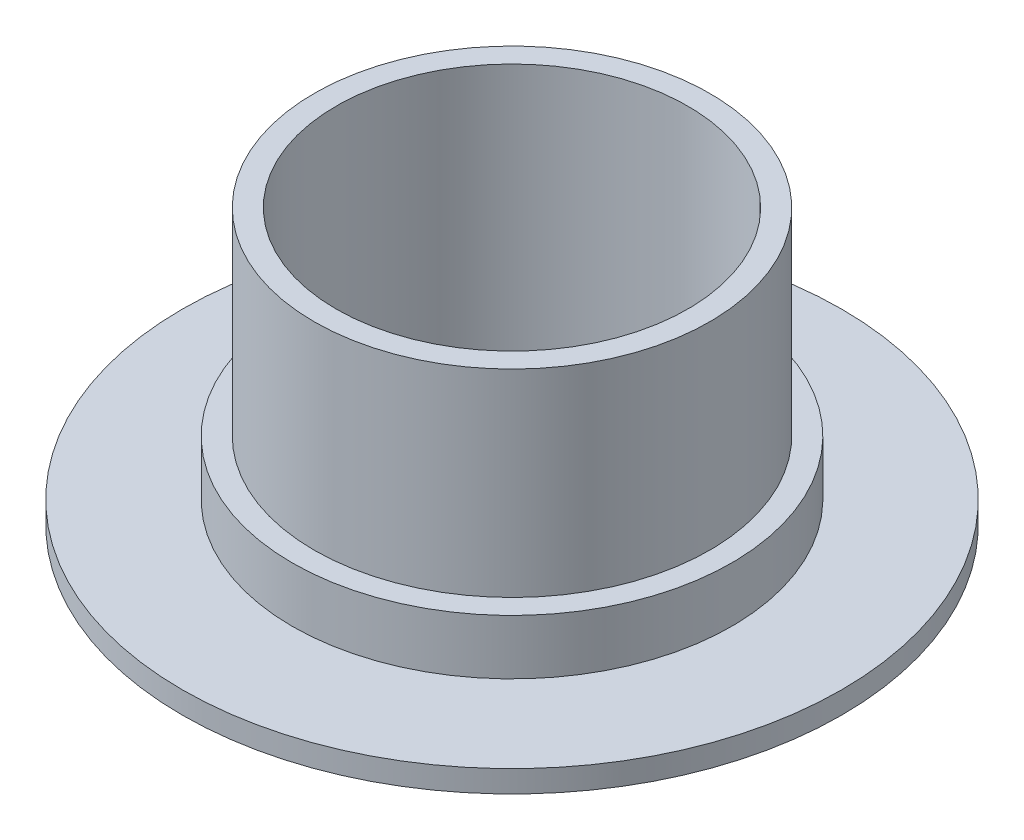
SolidWorks part; units mm, degrees
ref_plane "Front Plane" through (0, 0, 0) normal (0, 0, 1) x (1, 0, 0)
ref_plane "Top Plane" through (0, 0, 0) normal (0, 1, 0) x (1, 0, 0)
ref_plane "Right Plane" through (0, 0, 0) normal (1, 0, 0) x (0, 0, -1)
sketch "Sketch1" plane through (0, 0, 0) normal (0, 1, 0) x (1, 0, 0)
  circle A0 centre (0, 0) radius 30
  circle A1 centre (0, 0) radius 20
extrude "Boss-Extrude1" add sketch "Sketch1" along normal blind 2
sketch "Sketch2" plane through (0, 0, 0) normal (0, 1, 0) x (1, 0, 0)
  circle A0 centre (0, 0) radius 20
  circle A1 centre (0, 0) radius 18
extrude "Boss-Extrude2" add sketch "Sketch2" along normal blind 7
sketch "Sketch3" plane through (0, 0, 0) normal (0, 1, 0) x (1, 0, 0)
  circle A0 centre (0, 0) radius 18
  circle A1 centre (0, 0) radius 16
extrude "Boss-Extrude3" add sketch "Sketch3" along normal blind 25
